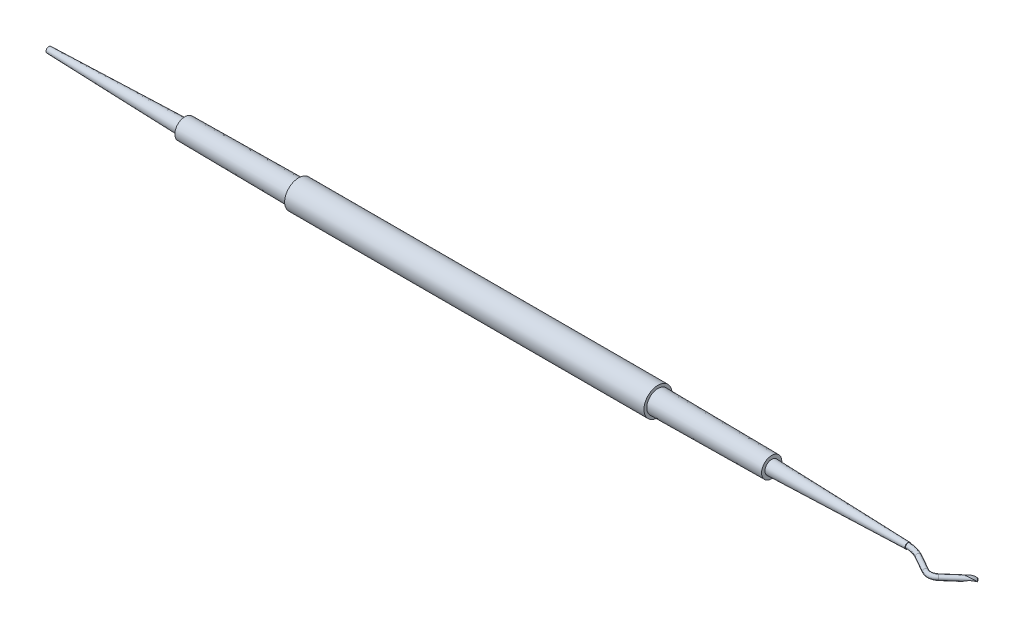
SolidWorks part; units mm, degrees
ref_plane "Front Plane" through (0, 0, 0) normal (0, 0, 1) x (1, 0, 0)
ref_plane "Top Plane" through (0, 0, 0) normal (0, 1, 0) x (1, 0, 0)
ref_plane "Right Plane" through (0, 0, 0) normal (1, 0, 0) x (0, 0, -1)
sketch "linear trace" plane through (0, 0, 0) normal (0, 1, 0) x (1, 0, 0)
  line L0 (544, 1224) -> (2720, 1224) construction
  line L1 (58.6476, 31.614) -> (61.5916, 29.9464)
  line L2 (67.5367, 33.5179) -> (63.697, 30.1609)
  line L3 (56.1008, 32.2852) -> (31.8502, 32.2852)
  line L4 (31.8502, 32.2852) -> (11.5916, 32.2852)
  line L8 (11.5916, 32.2852) -> (-52.4084, 32.2852)
  line L9 (61.5916, 31.5379) -> (61.5916, 26.5009) construction
  line L10 (58.6476, 34.5776) -> (58.6476, 27.8816) construction
  line L11 (31.8502, 35.1699) -> (31.8502, 28.7738) construction
  line L12 (66.6219, 34.4328) -> (68.5343, 32.5203) construction
  line L13 (11.5916, 37.7013) -> (11.5916, 27.1178) construction
  line L14 (-20.4084, 37.7013) -> (-20.4084, 23.3633) construction
  line L15 (56.1008, 34.5776) -> (56.1008, 28.9762) construction
  line L16 (-52.4084, 37.7013) -> (-52.4084, 27.1178) construction
  line L17 (-72.6669, 32.2852) -> (-52.4084, 32.2852)
  line L18 (-72.6669, 35.1699) -> (-72.6669, 28.7738) construction
  line L19 (-96.9175, 32.2852) -> (-72.6669, 32.2852)
  line L20 (-96.9175, 34.5776) -> (-96.9175, 28.9762) construction
  arc A0 (61.5916, 29.9464) -> (63.697, 30.1609) centre (62.4931, 31.5379) ccw
  arc A1 (56.1008, 32.2852) -> (58.6476, 31.614) centre (56.1008, 27.1178) cw
  point P27 (-20.4084, 32.2852)
ref_plane "Plane1" through (61.5916, 0, 0) normal (1, 0, 0) x (0, 0, -1)
ref_plane "Plane2" through (58.6476, 0, 0) normal (1, 0, 0) x (0, 0, -1)
ref_plane "Plane3" through (31.8502, 0, 0) normal (1, 0, 0) x (0, 0, -1)
ref_plane "Plane4" through (50.5273, 0, -50.5273) normal (0.7071, 0, -0.7071) x (0.7071, 0, 0.7071)
sketch "Sketch2" plane through (50.5273, 0, -50.5273) normal (0.7071, 0, -0.7071) x (0.7071, 0, 0.7071)
  circle A0 centre (24.0549, 0) radius 0.425
  point P4 (24.0549, 0)
  dimension "D1" = 0.85
sketch "Sketch3" plane through (61.5916, 0, 0) normal (1, 0, 0) x (0, 0, -1)
  circle A0 centre (29.9464, 0) radius 0.5
  dimension "D1" = 1
sketch "Sketch4" plane through (0, 0, 0) normal (0, 1, 0) x (1, 0, 0)
  line L2 (67.5367, 33.5179) -> (63.697, 30.1609) construction
  line L3 (67.5367, 33.5179) -> (63.697, 30.1609)
  line L4 (58.6476, 31.614) -> (61.5916, 29.9464) construction
  line L5 (58.6476, 31.614) -> (61.5916, 29.9464)
  arc A0 (61.5916, 29.9464) -> (63.697, 30.1609) centre (62.4931, 31.5379) ccw construction
  arc A1 (61.5916, 29.9464) -> (63.697, 30.1609) centre (62.4931, 31.5379) ccw
  arc A2 (58.6476, 31.614) -> (56.1008, 32.2852) centre (56.1008, 27.1178) ccw construction
  arc A3 (58.6476, 31.614) -> (56.1008, 32.2852) centre (56.1008, 27.1178) ccw
sweep "Sweep4" add profiles "Sketch2" path "Sketch4"
sketch "Sketch6" plane through (0, 0, 0) normal (0, 1, 0) x (1, 0, 0)
  line L0 (56.1008, 32.2852) -> (31.8502, 32.2852) construction
  line L1 (56.1008, 32.2852) -> (31.8502, 32.2852)
  line L2 (56.1008, 32.2852) -> (56.1008, 31.7852)
  line L3 (31.8502, 35.1699) -> (31.8502, 28.7738) construction
  line L4 (31.8502, 35.1699) -> (31.8502, 28.7738) construction
  line L5 (31.8502, 31.0852) -> (56.1008, 31.7852)
  line L6 (31.8502, 31.0852) -> (31.8502, 30.4852)
  line L7 (31.8502, 30.4852) -> (11.5916, 30.2852)
  line L8 (11.5916, 30.2852) -> (11.5916, 29.7852)
  line L9 (11.5916, 29.7852) -> (-52.4084, 29.7852)
  line L11 (11.5916, 32.2852) -> (-52.4084, 32.2852) construction
  line L15 (31.8502, 32.2852) -> (11.5916, 32.2852) construction
  line L17 (11.5916, 32.2852) -> (-52.4084, 32.2852)
  line L18 (-20.4084, 32.2852) -> (-20.4084, 29.7852) construction
  line L19 (31.8502, 32.2852) -> (11.5916, 32.2852)
  line L20 (11.5916, 32.2852) -> (11.5916, 27.6338) construction
  line L21 (-20.4084, 37.7013) -> (-20.4084, 23.3633) construction
  line L22 (-52.4084, 32.2852) -> (-52.4084, 27.6338) construction
  line L23 (-72.6669, 35.1699) -> (-72.6669, 28.7738) construction
  line L24 (-72.6669, 32.2852) -> (-52.4084, 32.2852)
  line L25 (-52.4084, 30.2852) -> (-52.4084, 29.7852)
  line L26 (-72.6669, 30.4852) -> (-52.4084, 30.2852)
  line L27 (-72.6669, 31.0852) -> (-72.6669, 30.4852)
  line L28 (-72.6669, 31.0852) -> (-96.9175, 31.7852)
  line L29 (-96.9175, 32.2852) -> (-96.9175, 31.7852)
  line L30 (-96.9175, 32.2852) -> (-72.6669, 32.2852)
  dimension "D1" = 0.5
  dimension "D2" = 1.2
  dimension "D3" = 2
  dimension "D4" = 1.8
  dimension "D5" = 2.5
revolve "Revolve1" add sketch "Sketch6" angle 360 about L8
ref_plane "Plane5" through (12.6499, 0, 14.4689) normal (-0.6582, 0, -0.7528) x (-0.7528, 0, 0.6582)
ref_plane "Plane6" through (12.979, 0, 14.8453) normal (-0.6582, 0, -0.7528) x (-0.7528, 0, 0.6582)
sketch "Sketch7" plane through (12.979, 0, 14.8453) normal (-0.6582, 0, -0.7528) x (-0.7528, 0, 0.6582)
  line L0 (804.1764, 1008.5492) -> (2890.5681, 390.5318) construction
  line L1 (-70.9069, -0.2587) -> (-70.4249, -0.4803)
  line L2 (-72.7165, -0.1669) -> (-72.7639, -0.2587)
  line L3 (-71.0972, 0.425) -> (-67.8057, 0.425) construction
  line L4 (-71.0972, 0.425) -> (-73.643, 0.425)
  line L5 (-73.643, 0.425) -> (-73.1771, -0.8091)
  line L6 (-73.1771, -0.8091) -> (-70.4249, -0.4803)
  line L7 (-67.8057, 0.425) -> (-72.906, 0.425) construction
  line L8 (-67.8057, 0.425) -> (-73.643, 0.425) construction
  arc A0 (-72.7639, -0.2587) -> (-70.9069, -0.2587) centre (-71.8354, -2.2779) cw
  arc A1 (-71.0972, 0.425) -> (-72.7165, -0.1669) centre (-71.0491, -2.2176) ccw
extrude "Cut-Extrude2" cut sketch "Sketch7" along normal blind 10
